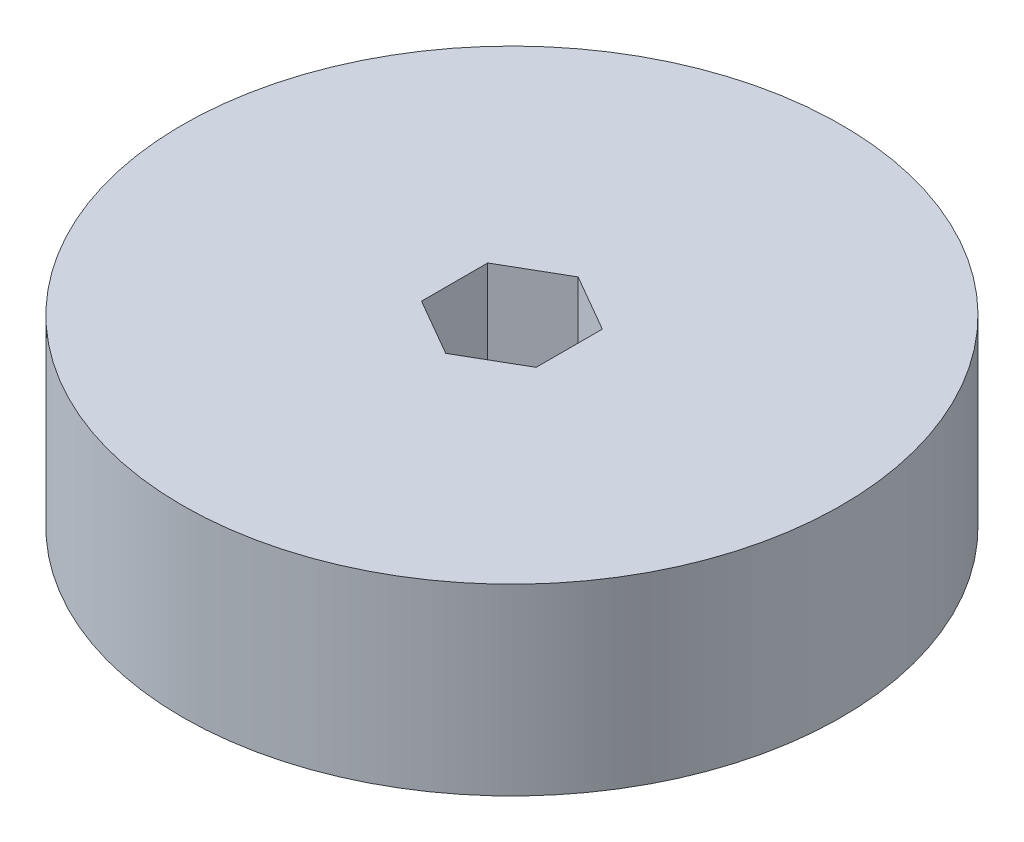
SolidWorks part; units mm, degrees
ref_plane "Front Plane" through (0, 0, 0) normal (0, 0, 1) x (1, 0, 0)
ref_plane "Top Plane" through (0, 0, 0) normal (0, 1, 0) x (1, 0, 0)
ref_plane "Right Plane" through (0, 0, 0) normal (1, 0, 0) x (0, 0, -1)
sketch "Sketch2" plane through (0, 0, 0) normal (0, 1, 0) x (1, 0, 0)
  line L1 (0, 7.3323) -> (-6.35, 3.6662)
  line L2 (-6.35, 3.6662) -> (-6.35, -3.6662)
  line L3 (-6.35, -3.6662) -> (0, -7.3323)
  line L4 (0, -7.3323) -> (6.35, -3.6662)
  line L5 (6.35, -3.6662) -> (6.35, 3.6662)
  line L6 (6.35, 3.6662) -> (0, 7.3323)
  circle A0 centre (0, 0) radius 36.5125
  circle A1 centre (0, 0) radius 6.35 construction
  dimension "D1" = 73.025
  dimension "D2" = 12.7
extrude "Boss-Extrude1" add sketch "Sketch2" along normal blind 20.32
